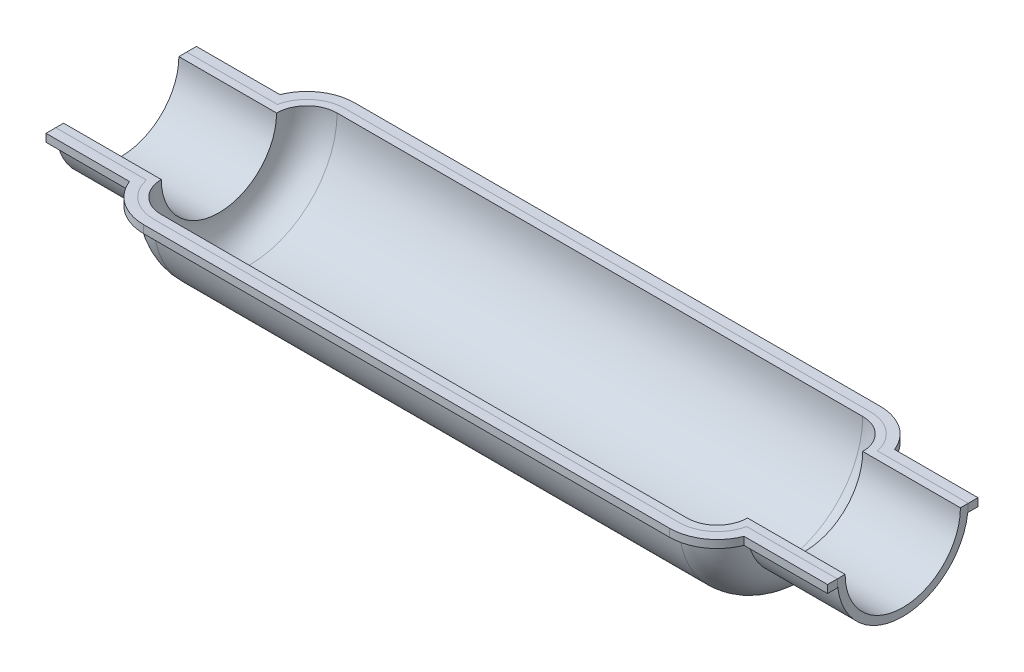
SolidWorks part; units mm, degrees
ref_plane "Front Plane" through (0, 0, 0) normal (0, 0, 1) x (1, 0, 0)
ref_plane "Top Plane" through (0, 0, 0) normal (0, 1, 0) x (1, 0, 0)
ref_plane "Right Plane" through (0, 0, 0) normal (1, 0, 0) x (0, 0, -1)
sketch "Sketch1" plane through (0, 0, 0) normal (0, 1, 0) x (1, 0, 0)
  line L0 (0, 0) -> (0, 59459.7927) construction
  line L1 (0, 0) -> (-59459.7927, 0) construction
  line L2 (-200, 29.5) -> (-150, 29.5)
  line L3 (-134.5, 45) -> (134.5, 45)
  line L4 (150, 29.5) -> (200, 29.5)
  line L5 (-200, 33.5) -> (-153.5853, 33.5)
  line L6 (-134.5, 49) -> (134.5, 49)
  line L7 (153.5853, 33.5) -> (200, 33.5)
  line L8 (-200, 33.5) -> (-200, 29.5)
  line L9 (200, 33.5) -> (200, 29.5)
  arc A0 (-150, 29.5) -> (-134.5, 45) centre (-134.5, 29.5) cw
  arc A1 (134.5, 45) -> (150, 29.5) centre (134.5, 29.5) cw
  arc A2 (-153.5853, 33.5) -> (-134.5, 49) centre (-134.5, 29.5) cw
  arc A3 (134.5, 49) -> (153.5853, 33.5) centre (134.5, 29.5) cw
  dimension "D1" = 300
  dimension "D2" = 50
  dimension "D3" = 45
  dimension "D4" = 29.5
  dimension "D5" = 4
revolve "Revolve1" add sketch "Sketch1" angle 180 about L1
sketch "Sketch3" plane through (0, 0, 0) normal (0, 1, 0) x (1, 0, 0)
  line L0 (200, 33.5) -> (153.5853, 33.5) construction
  line L1 (134.5, 49) -> (-134.5, 49) construction
  line L2 (-153.5853, 33.5) -> (-200, 33.5) construction
  line L3 (200, 33.5) -> (153.5853, 33.5)
  line L4 (134.5, 49) -> (-134.5, 49)
  line L5 (-153.5853, 33.5) -> (-200, 33.5)
  line L6 (200, 38.5) -> (157.2871, 38.5)
  line L7 (134.5, 54) -> (-134.5, 54)
  line L8 (-157.2871, 38.5) -> (-200, 38.5)
  line L9 (-200, 38.5) -> (-200, 33.5)
  line L10 (200, 38.5) -> (200, 33.5)
  line L11 (0, 0) -> (-50000, 0) construction
  line L12 (200, -38.5) -> (200, -33.5)
  line L13 (-200, -38.5) -> (-200, -33.5)
  line L14 (-157.2871, -38.5) -> (-200, -38.5)
  line L15 (134.5, -54) -> (-134.5, -54)
  line L16 (200, -38.5) -> (157.2871, -38.5)
  line L17 (-153.5853, -33.5) -> (-200, -33.5)
  line L18 (134.5, -49) -> (-134.5, -49)
  line L19 (200, -33.5) -> (153.5853, -33.5)
  arc A0 (153.5853, 33.5) -> (134.5, 49) centre (134.5, 29.5) ccw construction
  arc A1 (-134.5, 49) -> (-153.5853, 33.5) centre (-134.5, 29.5) ccw construction
  arc A2 (153.5853, 33.5) -> (134.5, 49) centre (134.5, 29.5) ccw
  arc A3 (-134.5, 49) -> (-153.5853, 33.5) centre (-134.5, 29.5) ccw
  arc A4 (157.2871, 38.5) -> (134.5, 54) centre (134.5, 29.5) ccw
  arc A5 (-134.5, 54) -> (-157.2871, 38.5) centre (-134.5, 29.5) ccw
  arc A6 (-134.5, -54) -> (-157.2871, -38.5) centre (-134.5, -29.5) cw
  arc A7 (157.2871, -38.5) -> (134.5, -54) centre (134.5, -29.5) cw
  arc A8 (-134.5, -49) -> (-153.5853, -33.5) centre (-134.5, -29.5) cw
  arc A9 (153.5853, -33.5) -> (134.5, -49) centre (134.5, -29.5) cw
  dimension "D1" = 5
extrude "Boss-Extrude2" add sketch "Sketch3" against normal blind 4 separate body
